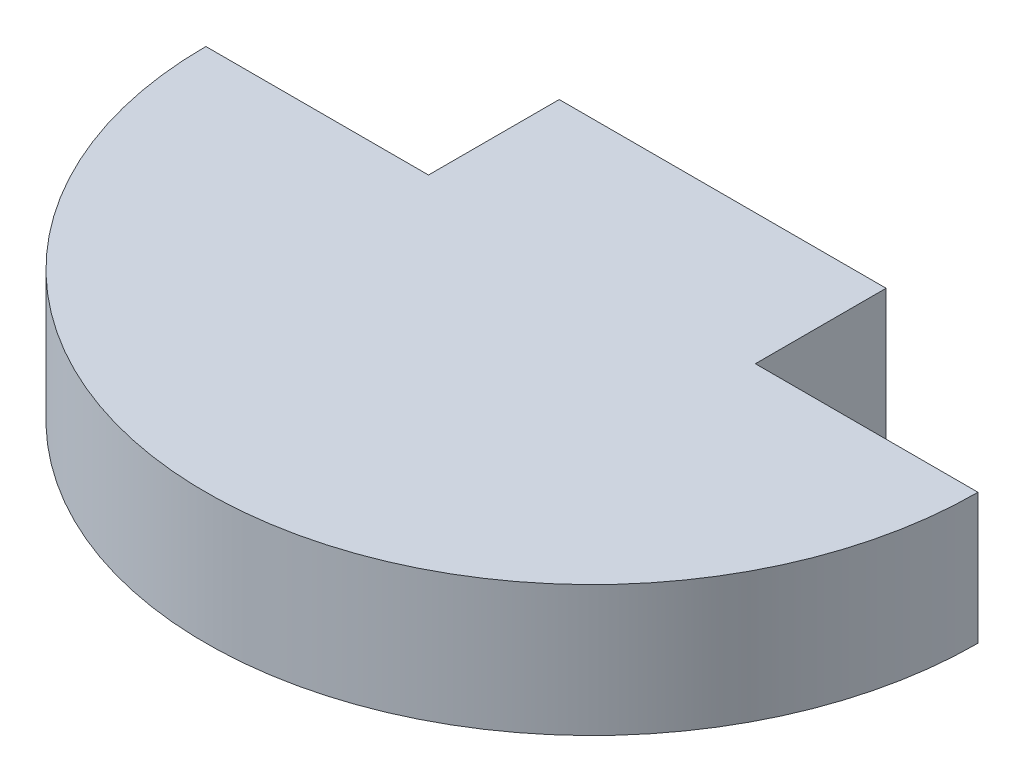
SolidWorks part; units mm, degrees
ref_plane "Front Plane" through (0, 0, 0) normal (0, 0, 1) x (1, 0, 0)
ref_plane "Top Plane" through (0, 0, 0) normal (0, 1, 0) x (1, 0, 0)
ref_plane "Right Plane" through (0, 0, 0) normal (1, 0, 0) x (0, 0, -1)
sketch "Sketch1" plane through (0, 0, 0) normal (0, 1, 0) x (1, 0, 0)
  circle A0 centre (0, 0) radius 15
  dimension "D1" = 30
extrude "Boss-Extrude1" add sketch "Sketch1" along normal blind 5.08 contours A0
sketch "Sketch2" plane through (0, 5.08, 0) normal (0, 1, 0) x (1, 0, 0)
  line L1 (15, 0) -> (-826.2161, 0)
  line L2 (15, 0) -> (15, 769.2498)
  line L3 (15, 769.2498) -> (-826.2161, 769.2498)
  line L4 (-826.2161, 0) -> (-826.2161, 769.2498)
  circle A0 centre (0, 0) radius 15 construction
extrude "Cut-Extrude1" cut sketch "Sketch2" against normal blind 5.08
sketch "Sketch3" plane through (0, 0, 0) normal (0, 0, -1) x (-1, 0, 0)
  line L0 (-15, 0) -> (-6.35, 0)
  line L1 (15, 0) -> (-15, 0) construction
  line L2 (-6.35, 0) -> (6.35, 0)
  line L3 (6.35, 0) -> (15, 0)
  line L4 (15, 5.08) -> (-15, 5.08) construction
  line L5 (-6.35, 0) -> (6.35, 0)
  line L6 (-6.35, 0) -> (-6.35, 5.08)
  line L7 (-6.35, 5.08) -> (6.35, 5.08)
  line L8 (6.35, 0) -> (6.35, 5.08)
  line M4 (15, 5.08) -> (-15, 5.08)
  line M6 (-15, 0) -> (15, 0)
  dimension "D1" = 12.7
extrude "Boss-Extrude2" add sketch "Sketch3" along normal blind 5.08 contours L8 L6 M6 M4
equation "\"MDFThickness\"= .2in"
equation "\"D1@Boss-Extrude1\"=\"MDFThickness\""
equation "\"D1@Boss-Extrude2\"=\"MDFThickness\""
